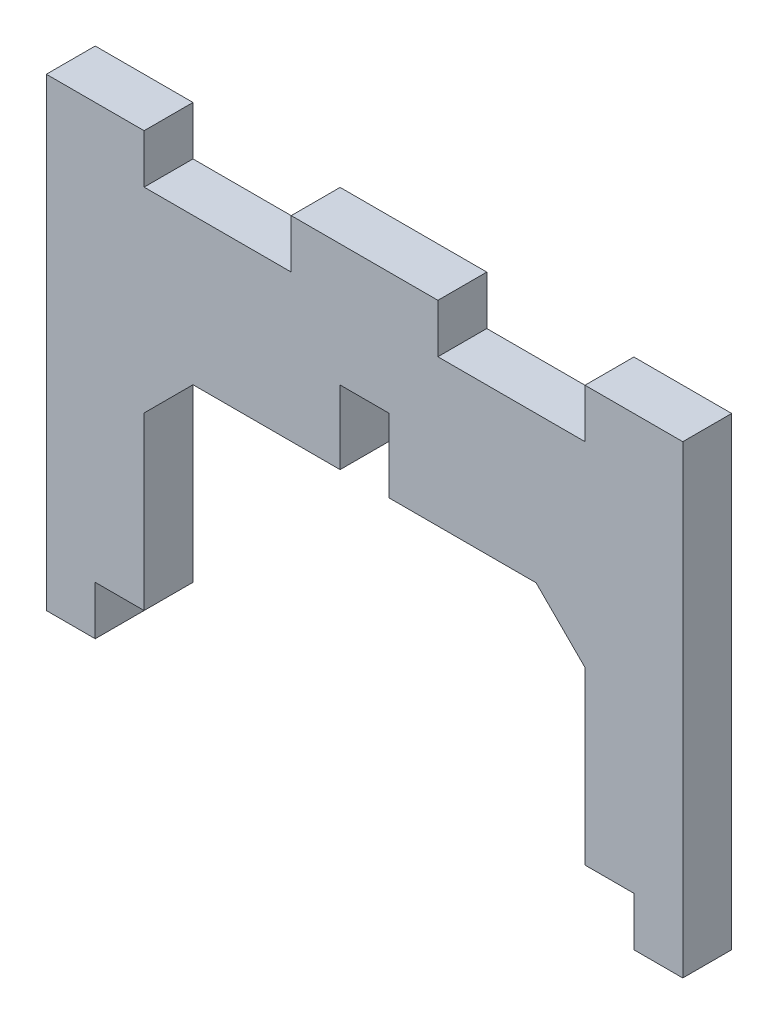
SolidWorks part; units mm, degrees
ref_plane "Front Plane" through (0, 0, 0) normal (0, 0, 1) x (1, 0, 0)
ref_plane "Top Plane" through (0, 0, 0) normal (0, 1, 0) x (1, 0, 0)
ref_plane "Right Plane" through (0, 0, 0) normal (1, 0, 0) x (0, 0, -1)
sketch "Sketch1" plane through (0, 0, 0) normal (0, 0, 1) x (1, 0, 0)
  line L0 (0, 0) -> (4, 0)
  line L1 (4, 0) -> (4, 4)
  line L2 (4, 4) -> (8, 4)
  line L3 (8, 4) -> (8, 22)
  line L4 (8, 22) -> (24.035, 22)
  line L5 (24.035, 22) -> (24.035, 28)
  line L6 (24.035, 28) -> (28.035, 28)
  line L7 (26.035, 28) -> (26.035, 34)
  line L8 (52.07, 34) -> (0, 34)
  line L9 (0, 34) -> (0, 0)
  line L10 (52.07, 34) -> (52.07, 0)
  line L11 (28.035, 22) -> (28.035, 28)
  line L12 (44.07, 22) -> (28.035, 22)
  line L13 (44.07, 4) -> (44.07, 22)
  line L14 (48.07, 4) -> (44.07, 4)
  line L15 (48.07, 0) -> (48.07, 4)
  line L16 (52.07, 0) -> (48.07, 0)
  dimension "D1" = 4
  dimension "D2" = 8
  dimension "D3" = 4
  dimension "D4" = 12
  dimension "D5" = 2
  dimension "D6" = 26.035
  dimension "D7" = 30
  dimension "D8" = 6
extrude "Boss-Extrude1" add sketch "Sketch1" along normal blind 4 contours L8 L9 L0 L1 L2 L3 L4 L5 L6 L7 | L16 L10 L8 L7 L6 L11 L12 L13 L14 L15
chamfer "Chamfer1" distance 4 angle 45 2 edges at (44.07, 22, 2) (8, 22, 2)
sketch "Sketch2" plane through (0, 0, 4) normal (0, 0, 1) x (1, 0, 0)
  line L0 (0, 34) -> (0, 38)
  line L1 (0, 38) -> (8, 38)
  line L2 (8, 38) -> (8, 34)
  line L3 (52.07, 34) -> (0, 34) construction
  line L4 (8, 34) -> (0, 34)
  line L6 (52.07, 34) -> (44.07, 34)
  line L7 (52.07, 34) -> (52.07, 38)
  line L8 (52.07, 38) -> (44.07, 38)
  line L9 (44.07, 34) -> (44.07, 38)
  line L10 (32.035, 34) -> (20.035, 34)
  line L11 (32.035, 34) -> (32.035, 38)
  line L12 (32.035, 38) -> (20.035, 38)
  line L13 (20.035, 34) -> (20.035, 38)
  line L19 (24.035, 28) -> (28.035, 28) construction
  point P20 (26.035, 28)
  point P21 (26.035, 38)
  dimension "D1" = 8
  dimension "D2" = 4
  dimension "D3" = 12
extrude "Boss-Extrude2" add sketch "Sketch2" against normal up to surface (4 mm away) up to face at (26.035, 14.6667, 0)
